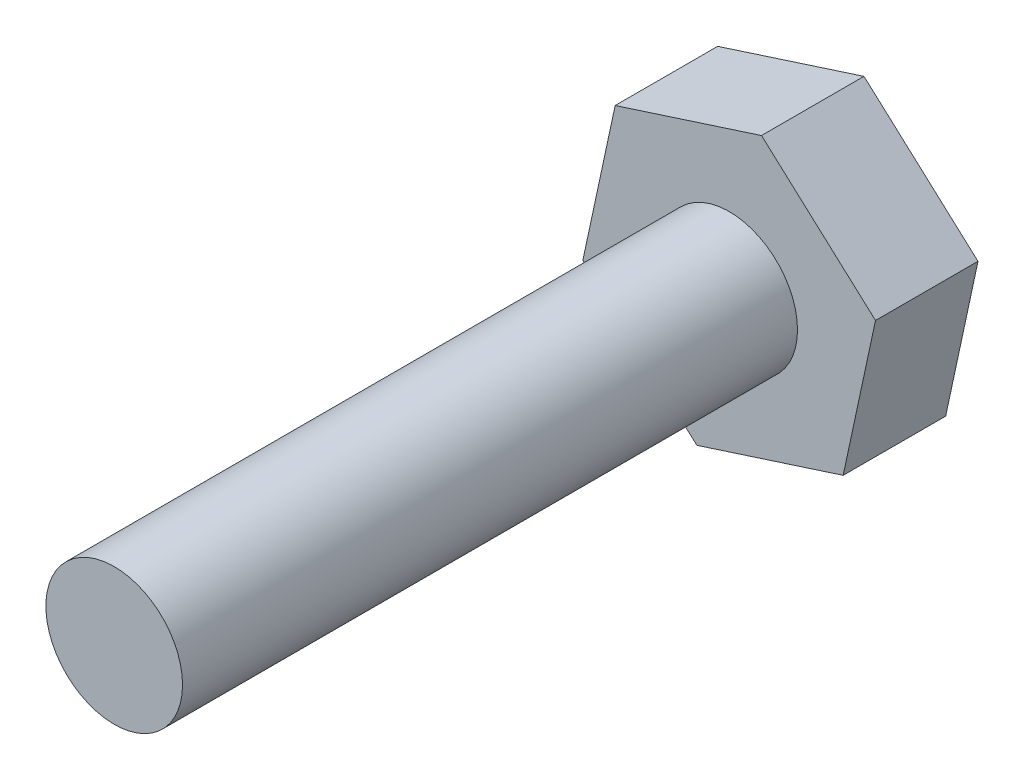
SolidWorks part; units mm, degrees
ref_plane "Front Plane" through (0, 0, 0) normal (0, 0, 1) x (1, 0, 0)
ref_plane "Top Plane" through (0, 0, 0) normal (0, 1, 0) x (1, 0, 0)
ref_plane "Right Plane" through (0, 0, 0) normal (1, 0, 0) x (0, 0, -1)
sketch "Sketch1" plane through (0, 0, 0) normal (0, 0, 1) x (1, 0, 0)
  line L1 (3.3368, -3.0192) -> (4.2831, 1.3802)
  line L2 (4.2831, 1.3802) -> (0.9463, 4.3994)
  line L3 (0.9463, 4.3994) -> (-3.3368, 3.0192)
  line L4 (-3.3368, 3.0192) -> (-4.2831, -1.3802)
  line L5 (-4.2831, -1.3802) -> (-0.9463, -4.3994)
  line L6 (-0.9463, -4.3994) -> (3.3368, -3.0192)
  circle A0 centre (0, 0) radius 3.8971 construction
  dimension "D1" = 4.5
extrude "Boss-Extrude1" add sketch "Sketch1" along normal blind 3
sketch "Sketch2" plane through (0, 0, 3) normal (0, 0, 1) x (1, 0, 0)
  circle A0 centre (0, 0) radius 2
  dimension "D1" = 4
extrude "Boss-Extrude2" add sketch "Sketch2" along normal blind 18
